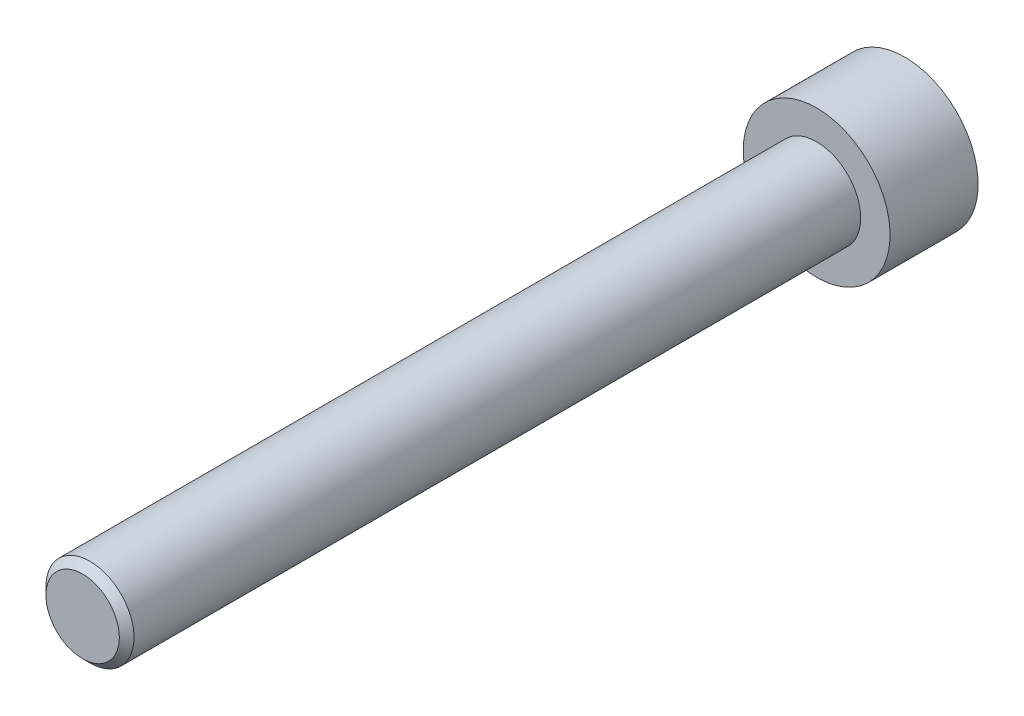
SolidWorks part; units mm, degrees
material "Acciaio al carbonio semplice"
ref_plane "Piano frontale" through (0, 0, 0) normal (0, 0, 1) x (1, 0, 0)
ref_plane "Piano superiore" through (0, 0, 0) normal (0, 1, 0) x (1, 0, 0)
ref_plane "Piano destro" through (0, 0, 0) normal (1, 0, 0) x (0, 0, -1)
sketch "Schizzo1" plane through (0, 0, 0) normal (0, 0, 1) x (1, 0, 0)
  circle A0 centre (0, 0) radius 3
  dimension "D1" = 6
extrude "Estrusione-Estrusione1" add sketch "Schizzo1" along normal blind 12 and the other way blind 44 from offset 11.2 offset against normal yes
chamfer "Smusso1" distance 0.5 angle 45 2 edges at (3, 0, -55.2) (3, 0, 0.8)
sketch "Schizzo4" plane through (0, 0, -55.2) normal (0, 0, -1) x (-1, 0, 0)
  circle A0 centre (0, 0) radius 5
  dimension "D1" = 10
extrude "Estrusione-Estrusione2" add sketch "Schizzo4" against normal blind 6
sketch "Schizzo5" plane through (0, 0, 0) normal (1, 0, 0) x (0, 0, -1)
  line L0 (0, 0) -> (23, 0)
  dimension "D1" = 23
sketch "Schizzo6" plane through (0, 0, -55.2) normal (0, 0, -1) x (-1, 0, 0)
  line L0 (0, 0) -> (0, 4.2016) construction
  line L1 (0, 0) -> (-6.9591, 0) construction
  line L2 (1.5, 3) -> (-1.5, 3)
  line L3 (-1.5, 3) -> (-3.2321, 0)
  line L4 (1.5, 3) -> (3.2321, 0)
  line L5 (-1.5, -3) -> (-3.2321, 0)
  line L6 (1.5, -3) -> (-1.5, -3)
  line L7 (1.5, -3) -> (3.2321, 0)
  point P8 (0, 3)
  dimension "D1" = 1.5
  dimension "D2" = 60
  dimension "D3" = 3
extrude "Taglio-Estrusione1" cut sketch "Schizzo6" against normal blind 2
sketch "Schizzo7" plane through (0, 0, 0.8) normal (0, 0, 1) x (1, 0, 0)
  line L0 (0, 0) -> (6.8312, -12.9071) construction
  line L1 (62.7469, -118.5557) -> (-64.4045, 121.6876) construction
